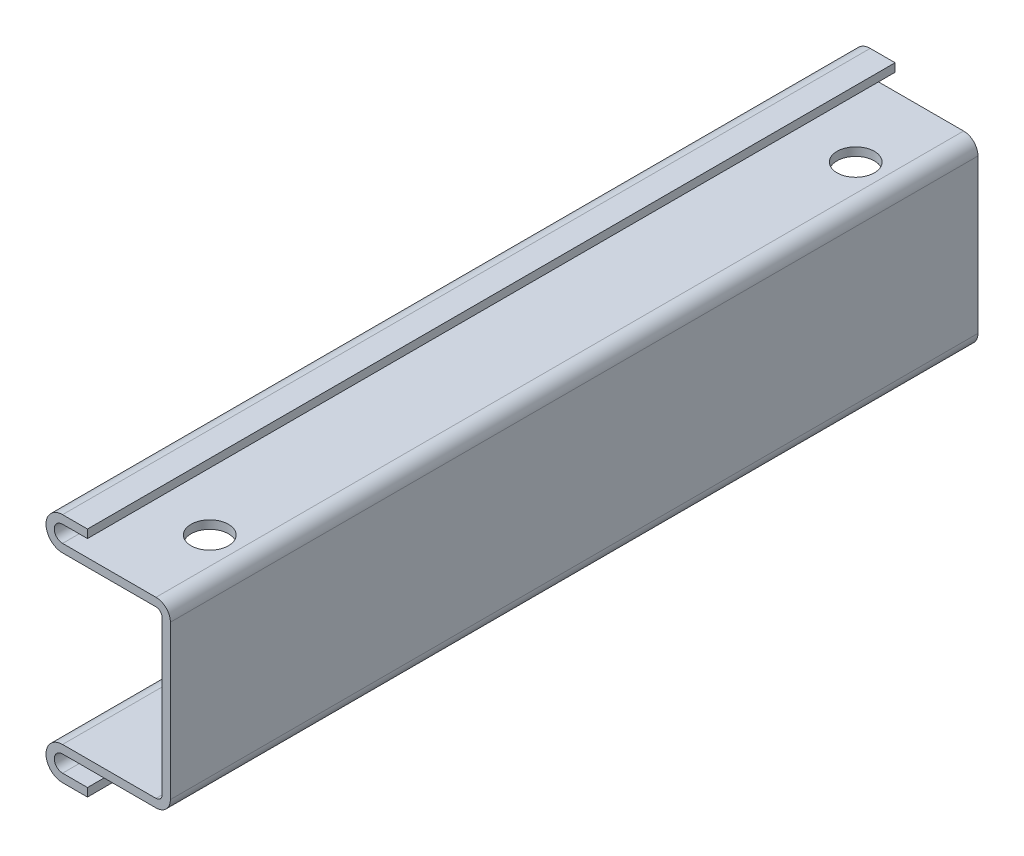
SolidWorks part; units mm, degrees
ref_plane "前视基准面" through (0, 0, 0) normal (0, 0, 1) x (1, 0, 0)
ref_plane "上视基准面" through (0, 0, 0) normal (0, 1, 0) x (1, 0, 0)
ref_plane "右视基准面" through (0, 0, 0) normal (1, 0, 0) x (0, 0, -1)
sketch "草图1" plane through (0, 0, 0) normal (0, 0, 1) x (1, 0, 0)
  line L1 (-13, 0.7366) -> (-1.7366, 0.7366)
  line L3 (-13, 1.7366) -> (-1.7366, 1.7366)
  line L6 (-1, 0) -> (-1, -18.5268)
  line L7 (0, 0) -> (0, -18.5268)
  line L11 (-1.7366, -19.2634) -> (-13, -19.2634)
  line L12 (-1.7366, -20.2634) -> (-13, -20.2634)
  line L13 (-10, 4.7366) -> (-13, 4.7366)
  line L14 (-10, 3.7366) -> (-10, 4.7366)
  line L15 (-10, 3.7366) -> (-13, 3.7366)
  line L17 (-13, -23.2634) -> (-10, -23.2634)
  line L18 (-10, -22.2634) -> (-10, -23.2634)
  line L19 (-13, -22.2634) -> (-10, -22.2634)
  arc A0 (-1, 0) -> (-1.7366, 0.7366) centre (-1.7366, 0) ccw
  arc A1 (0, 0) -> (-1.7366, 1.7366) centre (-1.7366, 0) ccw
  arc A2 (-13, -19.2634) -> (-13, -23.2634) centre (-13, -21.2634) ccw
  arc A3 (-13, -20.2634) -> (-13, -22.2634) centre (-13, -21.2634) ccw
  arc A4 (-1.7366, -19.2634) -> (-1, -18.5268) centre (-1.7366, -18.5268) ccw
  arc A5 (-1.7366, -20.2634) -> (0, -18.5268) centre (-1.7366, -18.5268) ccw
  arc A6 (-13, 4.7366) -> (-13, 0.7366) centre (-13, 2.7366) ccw
  arc A7 (-13, 3.7366) -> (-13, 1.7366) centre (-13, 2.7366) ccw
extrude "凸台-拉伸1" add sketch "草图1" along normal blind 97.4
sketch "草图2" plane through (0, -20.2634, 0) normal (0, -1, 0) x (1, 0, 0)
  line L0 (-1.7366, 48.7) -> (-38.3223, 48.7) construction
  line L1 (-1.7366, 97.4) -> (-1.7366, 0) construction
  line L2 (0, 97.4) -> (0, 0) construction
  circle A0 centre (-5, 87.65) radius 2.25
  circle A1 centre (-5, 9.75) radius 2.25
  dimension "D1" = 4.5
  dimension "D2" = 5
  dimension "D3" = 77.9
extrude "切除-拉伸1" cut sketch "草图2" against normal blind 97.4
